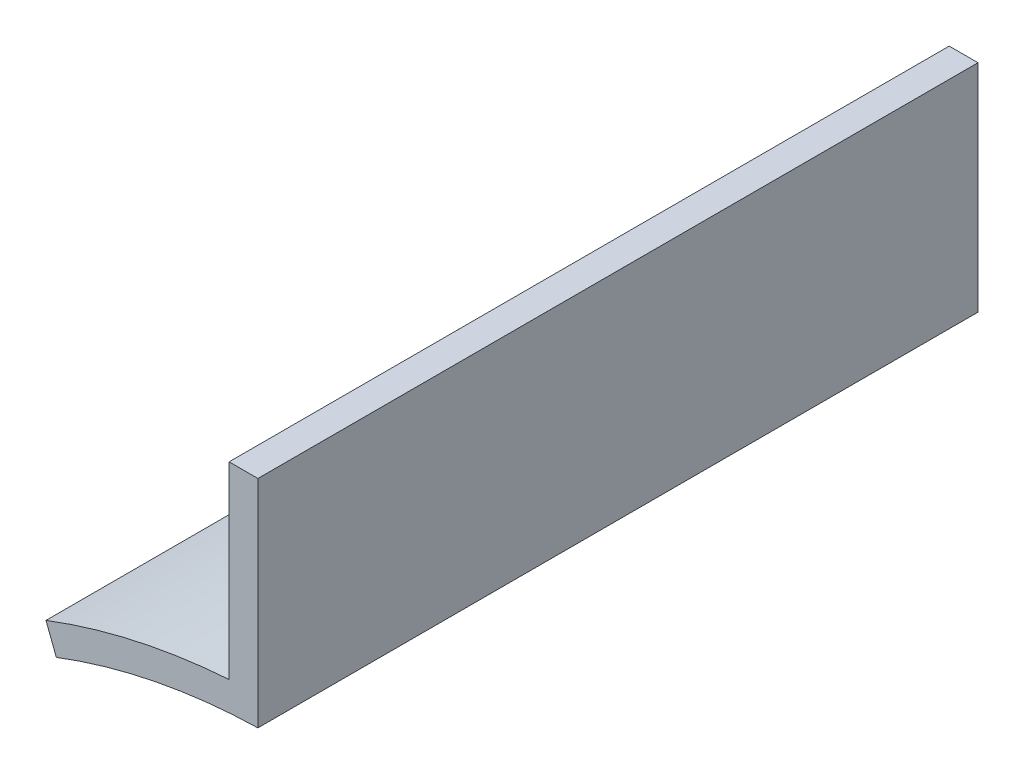
SolidWorks part; units mm, degrees
ref_plane "Front Plane" through (0, 0, 0) normal (0, 0, 1) x (1, 0, 0)
ref_plane "Top Plane" through (0, 0, 0) normal (0, 1, 0) x (1, 0, 0)
ref_plane "Right Plane" through (0, 0, 0) normal (1, 0, 0) x (0, 0, -1)
sketch "Sketch1" plane through (0, 0, 0) normal (0, 0, 1) x (1, 0, 0)
  line L0 (-1, 41.9881) -> (-1, 56.9881)
  line L1 (0, -5.5) -> (0, 5.5) construction
  line L2 (1, 41.9881) -> (1, 56.9881) construction
  line L7 (-3, 43.8976) -> (-3, 56.9881)
  line L8 (-15.7143, 41.0982) -> (-15, 39.2301)
  line L9 (-3, 56.9881) -> (-1, 56.9881)
  line L10 (1, 56.9881) -> (3, 56.9881) construction
  line L11 (15.7143, 41.0982) -> (15, 39.2301) construction
  line L12 (3, 43.8976) -> (3, 56.9881) construction
  arc A0 (-1, 41.9881) -> (-15, 39.2301) centre (0, 0) ccw construction
  arc A1 (-15, 39.2301) -> (-1, 41.9881) centre (0, 0) cw
  arc A4 (1, 41.9881) -> (14.9088, 39.2649) centre (0, 0) cw construction
  arc A5 (-1, 41.9881) -> (26.55, -32.5438) centre (0, 0) ccw construction
  arc A8 (26.55, -32.5438) -> (1, 41.9881) centre (0, 0) ccw construction
  arc A9 (-15.7143, 41.0982) -> (-3, 43.8976) centre (0, 0) cw
  arc A10 (15.7143, 41.0982) -> (3, 43.8976) centre (0, 0) ccw construction
  arc A16 (-26.4743, -32.6054) -> (-35.8628, -21.8601) centre (0, 0) cw [skipped]
  arc A20 (41.4743, -6.6247) -> (36.8628, -20.128) centre (0, 0) cw [skipped]
  point P3 (-15, 39.2301)
  point P4 (15, 39.2301)
  point P11 (41.4743, -6.6247)
  point P21 (0, 0)
  point P27 (-26.4743, -32.6054)
  point P30 (0, 0)
  point P58 (0, 0)
  dimension "D1" = 84
  dimension "D3" = 15
  dimension "D4" = 2
  dimension "D5" = 30
  dimension "D7" = 2
  dimension "D6" = 3
extrude "Boss-Extrude1" add sketch "Sketch1" along normal blind 50
mirror "Mirror2" [suppressed] about plane through (0, 0, 0) normal (1, 0, 0)
